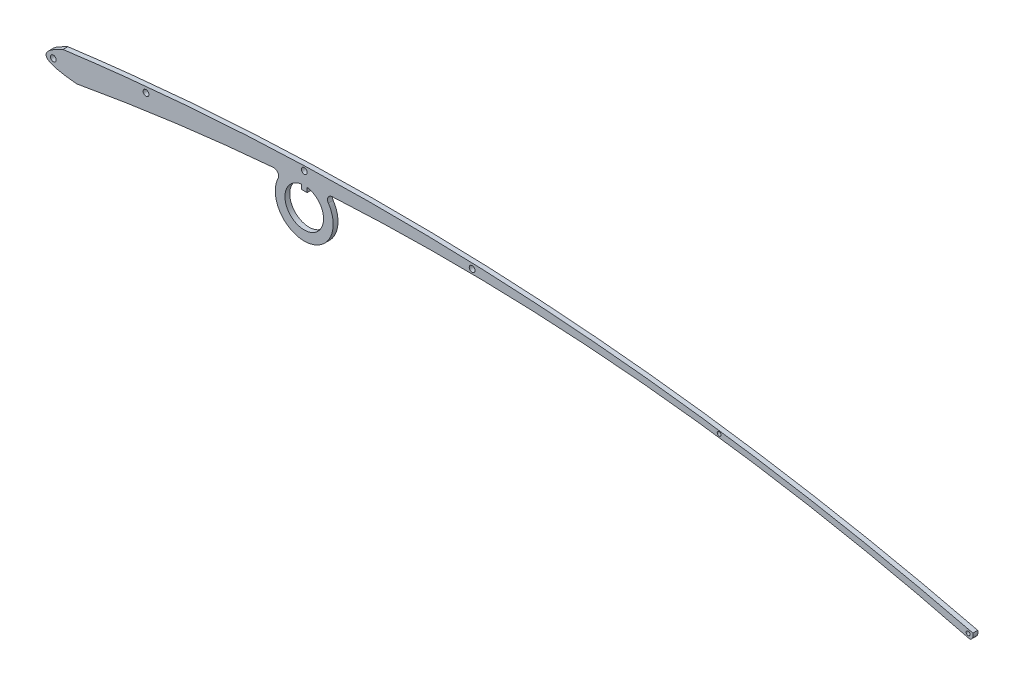
SolidWorks part; units mm, degrees
material "普通碳钢"
ref_plane "前视基准面" through (0, 0, 0) normal (0, 0, 1) x (1, 0, 0)
ref_plane "上视基准面" through (0, 0, 0) normal (0, 1, 0) x (1, 0, 0)
ref_plane "右视基准面" through (0, 0, 0) normal (1, 0, 0) x (0, 0, -1)
sketch "草图2" plane through (0, 0, 0) normal (0, 0, 1) x (1, 0, 0)
  arc A0 (94.3, -5.23) -> (94, -5.94) centre (93.7264, -5.406) cw
  spline S0 degree 2 poles (0, 0) (47.2733, 6.2558) (94.3, -5.23) knots 0 0 0 1 1 1
  spline S1 degree 2 poles (0, 0) (-4.1237, -1.8595) (1.4, -2.38) knots 0 0 0 1 1 1
  spline S2 degree 2 poles (1.4, -2.38) (47.9546, 5.9769) (94, -5.94) knots 0 0 0 1 1 1
  point P0 (26.37, 2.11)
  point P1 (94.3, -5.23)
  point P3 (94, -5.94)
  point P4 (42.19, 1.05)
  point P5 (-1.75, -1.25)
  point P6 (1.4, -2.38)
  dimension "D13" = 0.6
  dimension "D1" = 26.37
  dimension "D2" = 2.11
  dimension "D3" = 94.3
  dimension "D4" = 5.23
  dimension "D5" = 94
  dimension "D6" = 5.94
  dimension "D7" = 42.19
  dimension "D8" = 1.05
  dimension "D9" = 1.4
  dimension "D10" = 2.38
  dimension "D11" = 1.75
  dimension "D12" = 1.25
extrude "凸台-拉伸1" add sketch "草图2" along normal mid plane 0.5
sketch "草图3" plane through (0, 0, 0) normal (0, 0, 1) x (1, 0, 0)
  circle A0 centre (-1, -1.3) radius 0.3
  circle A1 centre (8.6, 0.4) radius 0.3
  circle A2 centre (25, 1.6) radius 0.3
  circle A3 centre (42.4, 1.5) radius 0.3
  circle A4 centre (68, -0.5) radius 0.2
  circle A5 centre (93.8, -5.5) radius 0.2
  dimension "D1" = 0.4
  dimension "D2" = 0.6
  dimension "D3" = 1.3
  dimension "D4" = 1
  dimension "D5" = 8.6
  dimension "D6" = 0.4
  dimension "D7" = 25
  dimension "D8" = 1.6
  dimension "D9" = 43.4
  dimension "D10" = 1.5
  dimension "D11" = 68
  dimension "D12" = 0.5
  dimension "D13" = 93.8
  dimension "D14" = 5.5
extrude "切除-拉伸1" cut sketch "草图3" against normal mid plane 0.5
sketch "草图4" plane through (0, 0, 0) normal (0, 0, 1) x (1, 0, 0)
  line L0 (25, -1.7) -> (25, -0.2) construction
  line L2 (24.7, 0.2774) -> (24.7, -0.2)
  line L3 (24.7, -0.2) -> (25.3, -0.2)
  line L4 (25.3, 0.2774) -> (25.3, -0.2)
  arc A0 (24.7, 0.2774) -> (25.3, 0.2774) centre (25, -1.7) ccw
  arc A1 (22.8546, 0.397) -> (26.8328, 0.675) centre (25, -1.7) ccw
  parabola Q0 (1.4, -2.38) -> (94, -5.94) focus (42.352, -104.8101) apex (45.0091, 0.998) construction
  parabola Q1 (22.8546, 0.397) -> (26.8328, 0.675) focus (42.352, -104.8101) apex (45.0091, 0.998)
  dimension "D1" = 3
  dimension "D2" = 4
  dimension "D3" = 25
  dimension "D4" = 1.7
  dimension "D5" = 0.6
  dimension "D6" = 0.5
extrude "凸台-拉伸2" add sketch "草图4" along normal mid plane 0.5
fillet "圆角1" radius 0.5 2 edges at (26.8328, 0.675, 0) (22.8546, 0.397, 0)
